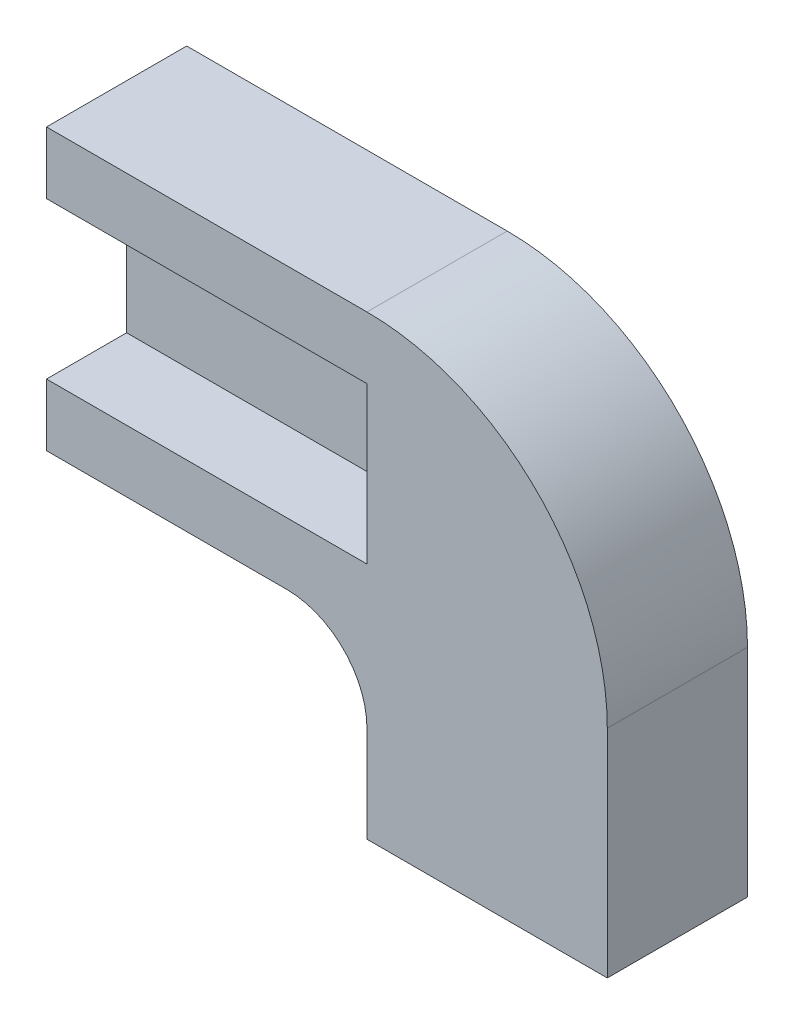
SolidWorks part; units mm, degrees
ref_plane "Front Plane" through (0, 0, 0) normal (0, 0, 1) x (1, 0, 0)
ref_plane "Top Plane" through (0, 0, 0) normal (0, 1, 0) x (1, 0, 0)
ref_plane "Right Plane" through (0, 0, 0) normal (1, 0, 0) x (0, 0, -1)
ref_plane "Plane1" through (0, 0, 4.445) normal (0, 0, 1) x (1, 0, 0)
sketch "Sketch1" plane through (0, 0, 4.445) normal (0, 0, 1) x (1, 0, 0)
  line L0 (0, 0) -> (0, -14.478)
  line L1 (0, -14.478) -> (17.78, -14.478)
  line L2 (17.78, -14.478) -> (17.78, 0)
  line L3 (17.78, 0) -> (0, 0)
extrude "Boss-Extrude1" add sketch "Sketch1" against normal blind 4.445
sketch "Sketch2" plane through (0, 0, 0) normal (0, 0, -1) x (-1, 0, 0)
  line L0 (0, -8.89) -> (-10.16, -8.89)
  line L1 (-10.16, -8.89) -> (-10.16, -14.478)
  line L2 (-10.16, -14.478) -> (0, -14.478)
  line L3 (0, -14.478) -> (0, -8.89)
extrude "Cut-Extrude1" cut sketch "Sketch2" against normal through all
sketch "Sketch3" plane through (0, 0, 4.445) normal (0, 0, 1) x (1, 0, 0)
  line L0 (10.16, -1.9685) -> (0, -1.9685)
  line L1 (0, -1.9685) -> (0, -6.9215)
  line L2 (0, -6.9215) -> (10.16, -6.9215)
  line L3 (10.16, -6.9215) -> (10.16, -1.9685)
extrude "Cut-Extrude2" cut sketch "Sketch3" against normal blind 2.54
fillet "Fillet1" radius 2.54 1 edges at (10.16, -8.89, 2.2225)
fillet "Fillet2" radius 7.62 1 edges at (17.78, 0, 2.2225)
